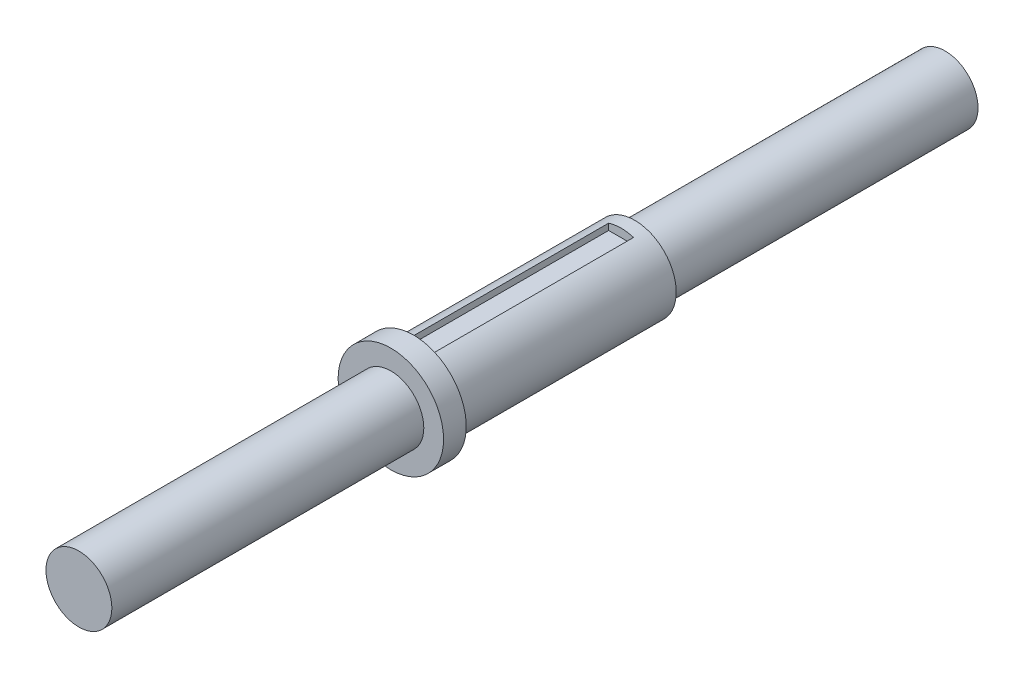
SolidWorks part; units mm, degrees
material "AISI 304"
ref_plane "Front Plane" through (0, 0, 0) normal (0, 0, 1) x (1, 0, 0)
ref_plane "Top Plane" through (0, 0, 0) normal (0, 1, 0) x (1, 0, 0)
ref_plane "Right Plane" through (0, 0, 0) normal (1, 0, 0) x (0, 0, -1)
sketch "Sketch1" plane through (0, 0, 0) normal (0, 0, 1) x (1, 0, 0)
  circle A0 centre (0, 0) radius 6.35
  dimension "D1" = 12.7
extrude "Boss-Extrude1" add sketch "Sketch1" along normal blind 160.3
sketch "Sketch2" plane through (0, 0, 0) normal (0, 1, 0) x (1, 0, 0)
  line L0 (0, 0) -> (0, 5.2173) construction
sketch "Sketch3" plane through (0, 0, 0) normal (0, 0, -1) x (-1, 0, 0)
  circle A0 centre (0, 0) radius 5
  dimension "D1" = 10
extrude "Cut-Extrude2" cut sketch "Sketch3" against normal blind 120 flip side to cut
sketch "Sketch4" plane through (0, 0, 160.3) normal (0, 0, 1) x (1, 0, 0)
  circle A0 centre (0, 0) radius 3.9688
  dimension "D1" = 7.9375
extrude "Cut-Extrude3" cut sketch "Sketch4" against normal blind 37.57 flip side to cut
sketch "Sketch5" plane through (0, 0, 0) normal (0, 0, -1) x (-1, 0, 0)
  circle A0 centre (0, 0) radius 3.97
  dimension "D1" = 7.94
extrude "Cut-Extrude4" cut sketch "Sketch5" against normal blind 93.36 flip side to cut
sketch "Sketch6" plane through (0, 0, 0) normal (0, 0, -1) x (-1, 0, 0)
  circle A0 centre (0, 0) radius 3.9688
  dimension "D1" = 7.9375
ref_plane "Plane1" through (0, 5, 0) normal (0, 1, 0) x (1, 0, 0)
sketch "Sketch9" plane through (0, 5, 0) normal (0, 1, 0) x (1, 0, 0)
  line L0 (0, -120) -> (0, -84.3327) construction
  line L1 (1.5, -120) -> (1.5, -95)
  line L2 (1.5, -95) -> (-1.5, -95)
  line L3 (-1.5, -95) -> (-1.5, -120)
  line L4 (1.5, -120) -> (-1.5, -120)
  line L6 (5, -120) -> (-5, -120) construction
  point P6 (0, -95)
  dimension "D1" = 3
  dimension "D2" = 25
extrude "Cut-Extrude6" cut sketch "Sketch9" against normal blind 1
ref_plane "Plane2" through (0, -5, 0) normal (0, -1, 0) x (-1, 0, 0)
sketch "Sketch11" plane through (0, -5, 0) normal (0, -1, 0) x (-1, 0, 0)
  line L0 (1.8837, -120.0203) -> (-1.8837, -120.0203)
  line L1 (-1.8837, -120.0203) -> (-1.8837, -95.0203)
  line L2 (-1.8837, -95.0203) -> (1.8837, -95.0203)
  line L3 (1.8837, -95.0203) -> (1.8837, -120.0203)
  line L4 (0, -120.0203) -> (0, -86.994) construction
  point P7 (0, -95.0203)
  point P8 (0, -120.0203)
  dimension "D1" = 25
extrude "Cut-Extrude7" cut sketch "Sketch11" against normal blind 1
sketch "Sketch12" plane through (0, 0, 0) normal (0, 0, -1) x (-1, 0, 0)
  circle A0 centre (0, 0) radius 15.9147
extrude "Cut-Extrude8" cut sketch "Sketch12" against normal blind 55.98
